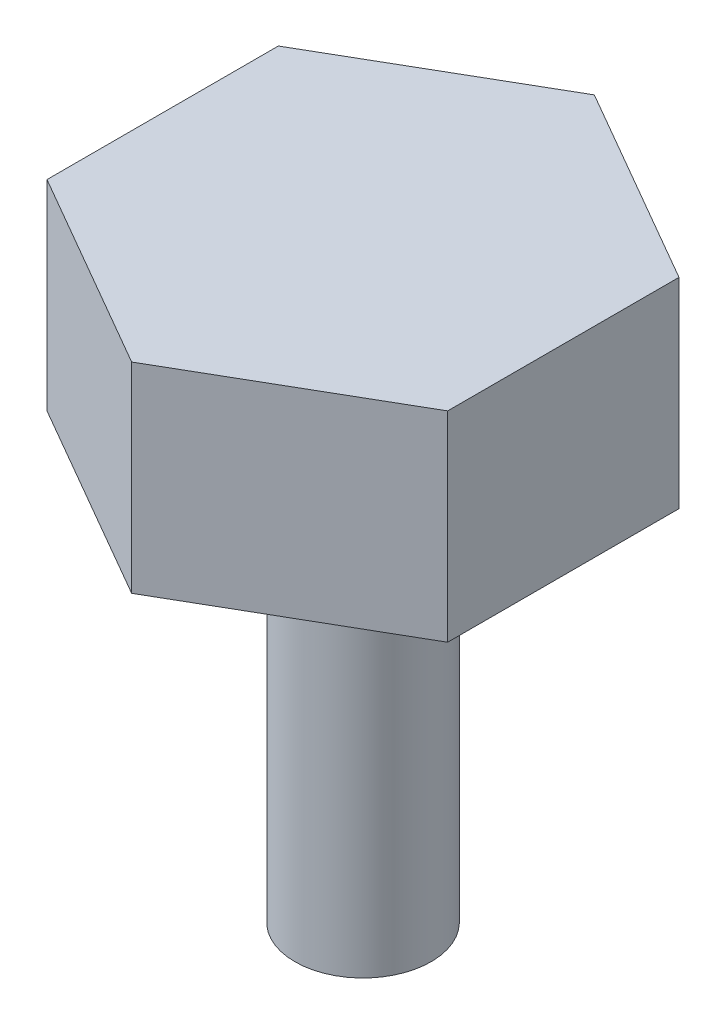
SolidWorks part; units mm, degrees
ref_plane "Front Plane" through (0, 0, 0) normal (0, 0, 1) x (1, 0, 0)
ref_plane "Top Plane" through (0, 0, 0) normal (0, 1, 0) x (1, 0, 0)
ref_plane "Right Plane" through (0, 0, 0) normal (1, 0, 0) x (0, 0, -1)
sketch "Sketch1" plane through (0, 0, 0) normal (0, 1, 0) x (1, 0, 0)
  circle A0 centre (0, 0) radius 2.159
  dimension "D1" = 4.318
extrude "Boss-Extrude1" add sketch "Sketch1" along normal blind 12.7
sketch "Sketch2" plane through (0, 12.7, 0) normal (0, 1, 0) x (1, 0, 0)
  line L1 (0, -7.3323) -> (6.35, -3.6662)
  line L2 (6.35, -3.6662) -> (6.35, 3.6662)
  line L3 (6.35, 3.6662) -> (0, 7.3323)
  line L4 (0, 7.3323) -> (-6.35, 3.6662)
  line L5 (-6.35, 3.6662) -> (-6.35, -3.6662)
  line L6 (-6.35, -3.6662) -> (0, -7.3323)
  circle A0 centre (0, 0) radius 6.35 construction
  dimension "D1" = 12.7
extrude "Boss-Extrude2" add sketch "Sketch2" along normal blind 6.35
